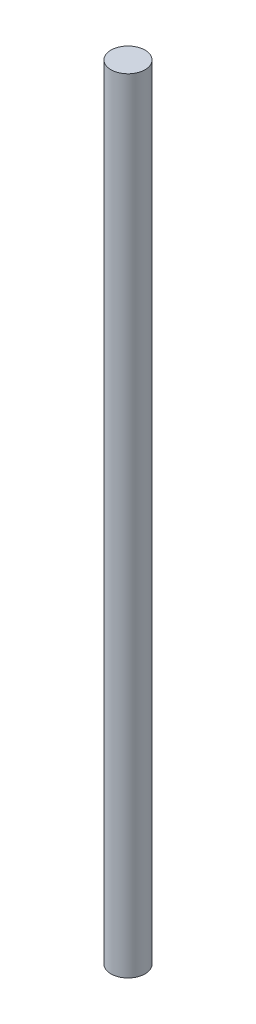
SolidWorks part; units mm, degrees
ref_plane "Front Plane" through (0, 0, 0) normal (0, 0, 1) x (1, 0, 0)
ref_plane "Top Plane" through (0, 0, 0) normal (0, 1, 0) x (1, 0, 0)
ref_plane "Right Plane" through (0, 0, 0) normal (1, 0, 0) x (0, 0, -1)
sketch "Sketch1" plane through (0, 0, 0) normal (0, 1, 0) x (1, 0, 0)
  circle A0 centre (0, 0) radius 12.7
  dimension "D1" = 25.4
extrude "Boss-Extrude1" add sketch "Sketch1" along normal blind 584.2
